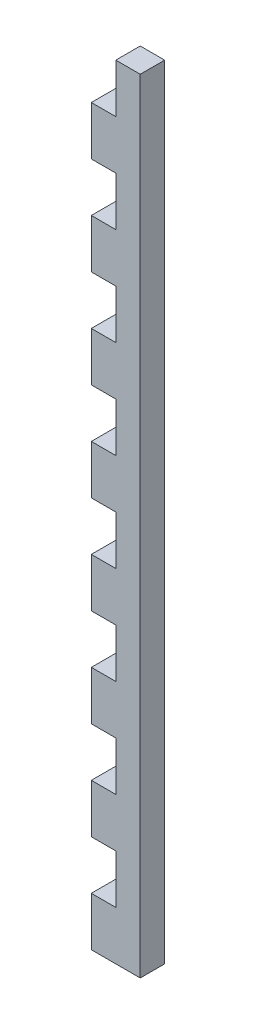
SolidWorks part; units mm, degrees
material "Balsa"
ref_plane "Alzado" through (0, 0, 0) normal (0, 0, 1) x (1, 0, 0)
ref_plane "Planta" through (0, 0, 0) normal (0, 1, 0) x (1, 0, 0)
ref_plane "Vista lateral" through (0, 0, 0) normal (1, 0, 0) x (0, 0, -1)
sketch "Croquis1" plane through (0, 0, 0) normal (0, 0, 1) x (1, 0, 0)
  line L0 (-10.5031, 53.1111) -> (-10.5031, 43.1111)
  line L1 (-10.5031, 73.1111) -> (-0.5031, 73.1111)
  line L2 (-10.5031, 73.1111) -> (-10.5031, -86.8889)
  line L3 (-10.5031, -86.8889) -> (-0.5031, -86.8889)
  line L4 (-0.5031, 73.1111) -> (-0.5031, -86.8889)
  line L5 (-10.5031, 73.1111) -> (-5.5031, 73.1111)
  line L6 (-10.5031, 73.1111) -> (-10.5031, 63.1111)
  line L7 (-10.5031, 63.1111) -> (-5.5031, 63.1111)
  line L8 (-5.5031, 73.1111) -> (-5.5031, 63.1111)
  line L9 (-10.5031, 53.1111) -> (-5.5031, 53.1111)
  line L10 (-5.5031, 53.1111) -> (-5.5031, 43.1111)
  line L11 (-10.5031, 43.1111) -> (-5.5031, 43.1111)
  line L12 (-10.5031, 33.1111) -> (-10.5031, 23.1111)
  line L13 (-10.5031, 33.1111) -> (-5.5031, 33.1111)
  line L14 (-5.5031, 33.1111) -> (-5.5031, 23.1111)
  line L15 (-10.5031, 23.1111) -> (-5.5031, 23.1111)
  line L16 (-10.5031, 13.1111) -> (-10.5031, 3.1111)
  line L17 (-10.5031, 13.1111) -> (-5.5031, 13.1111)
  line L18 (-5.5031, 13.1111) -> (-5.5031, 3.1111)
  line L19 (-10.5031, 3.1111) -> (-5.5031, 3.1111)
  line L20 (-10.5031, -6.8889) -> (-10.5031, -16.8889)
  line L21 (-10.5031, -6.8889) -> (-5.5031, -6.8889)
  line L22 (-5.5031, -6.8889) -> (-5.5031, -16.8889)
  line L23 (-10.5031, -16.8889) -> (-5.5031, -16.8889)
  line L24 (-10.5031, -26.8889) -> (-10.5031, -36.8889)
  line L25 (-10.5031, -26.8889) -> (-5.5031, -26.8889)
  line L26 (-5.5031, -26.8889) -> (-5.5031, -36.8889)
  line L27 (-10.5031, -36.8889) -> (-5.5031, -36.8889)
  line L28 (-10.5031, -46.8889) -> (-10.5031, -56.8889)
  line L29 (-10.5031, -46.8889) -> (-5.5031, -46.8889)
  line L30 (-5.5031, -46.8889) -> (-5.5031, -56.8889)
  line L31 (-10.5031, -56.8889) -> (-5.5031, -56.8889)
  line L32 (-10.5031, -66.8889) -> (-10.5031, -76.8889)
  line L33 (-10.5031, -66.8889) -> (-5.5031, -66.8889)
  line L34 (-5.5031, -66.8889) -> (-5.5031, -76.8889)
  line L35 (-10.5031, -76.8889) -> (-5.5031, -76.8889)
  dimension "D1" = 160
  dimension "D2" = 10
  dimension "D3" = 10
  dimension "D4" = 5
  dimension "D5" = 8
extrude "Saliente-Extruir1" add sketch "Croquis1" along normal blind 5 contours L35 L2 L3 L4 L1 L8 L7 L9 L10 L11 L13 L14 L15 L17 L18 L19 L21 L22 L23 L25 L26 L27 L29 L30 L31 L33 L34
